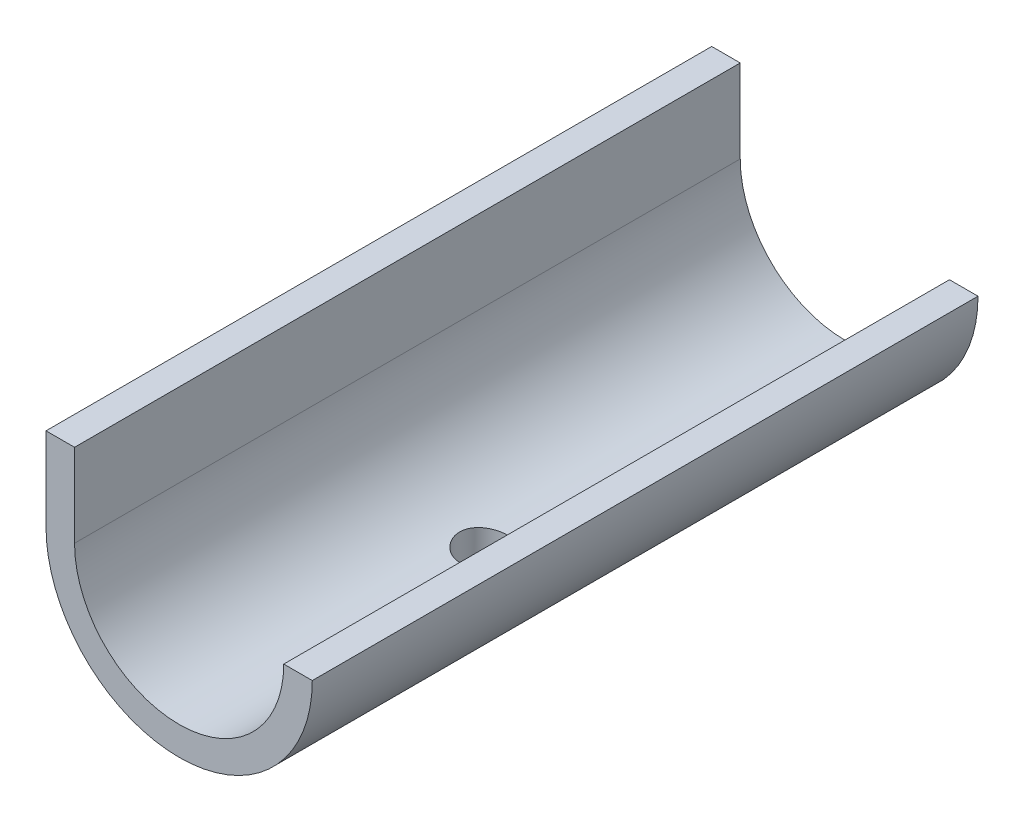
SolidWorks part; units mm, degrees
ref_plane "Front Plane" through (0, 0, 0) normal (0, 0, 1) x (1, 0, 0)
ref_plane "Top Plane" through (0, 0, 0) normal (0, 1, 0) x (1, 0, 0)
ref_plane "Right Plane" through (0, 0, 0) normal (1, 0, 0) x (0, 0, -1)
sketch "Sketch2" plane through (0, 0, 0) normal (0, 0, 1) x (1, 0, 0)
  circle A0 centre (0, 0) radius 14
  dimension "D1" = 28
extrude "Boss-Extrude1" add sketch "Sketch2" along normal blind 70 contours A0
sketch "Sketch3" plane through (0, 0, 70) normal (0, 0, 1) x (1, 0, 0)
  circle A0 centre (0, 0) radius 11
  dimension "D1" = 22
extrude "Cut-Extrude1" cut sketch "Sketch3" against normal through all
sketch "Sketch4" plane through (0, 0, 70) normal (0, 0, 1) x (1, 0, 0)
  line L1 (-16.0294, 0) -> (16.2012, 0)
  line L2 (-16.0294, 0) -> (-16.0294, 15.2787)
  line L3 (-16.0294, 15.2787) -> (16.2012, 15.2787)
  line L4 (16.2012, 0) -> (16.2012, 15.2787)
extrude "Cut-Extrude2" cut sketch "Sketch4" against normal through all
sketch "Sketch5" plane through (0, 0, 70) normal (0, 0, 1) x (1, 0, 0)
  line L0 (-14, 0) -> (-11, 0)
  line L1 (-11, 0) -> (-11, 8.7408)
  line L2 (-11, 8.7408) -> (-14, 8.7408)
  line L3 (-14, 8.7408) -> (-14, 0)
extrude "Boss-Extrude3" add sketch "Sketch5" against normal blind 70 contours L3 L0 L1 L2
sketch "Sketch6" plane through (-14, 0, 0) normal (-1, 0, 0) x (0, 0, 1)
  line L0 (0, 8.7408) -> (70, 8.7408)
  line L1 (70, 8.7408) -> (70, 4.7408)
  line L2 (70, 8.7408) -> (70, 0) construction
  line L3 (70, 4.7408) -> (0, 4.7408)
  line L4 (0, 8.7408) -> (0, 0) construction
  line L5 (0, 4.7408) -> (0, 8.7408)
  dimension "D1" = 4
sketch "Sketch7" plane through (0, 0, 0) normal (0, 1, 0) x (1, 0, 0)
  line L0 (-11, 0) -> (-11, -70) construction
  line L1 (11, 0) -> (-11, 0) construction
  circle A0 centre (0, -38) radius 2.5
  dimension "D1" = 5
  dimension "D2" = 11
  dimension "D3" = 38
extrude "Cut-Extrude3" cut sketch "Sketch7" against normal through all
